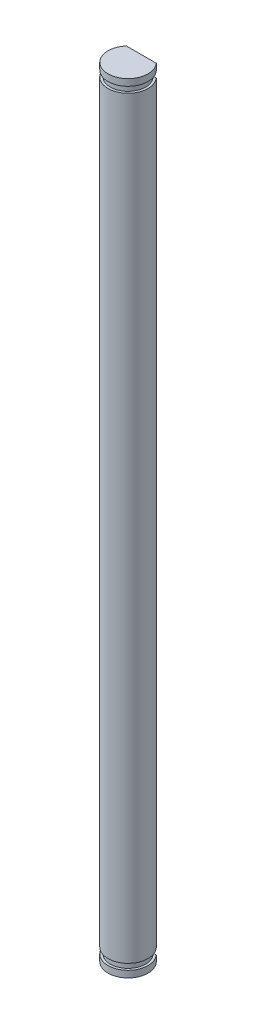
SolidWorks part; units mm, degrees
ref_plane "Front Plane" through (0, 0, 0) normal (0, 0, 1) x (1, 0, 0)
ref_plane "Top Plane" through (0, 0, 0) normal (0, 1, 0) x (1, 0, 0)
ref_plane "Right Plane" through (0, 0, 0) normal (1, 0, 0) x (0, 0, -1)
sketch "Sketch1" plane through (0, 0, 0) normal (0, 1, 0) x (1, 0, 0)
  line L0 (-2.2361, 2) -> (2.2361, 2)
  arc A0 (2.2361, 2) -> (-2.2361, 2) centre (0, 0) cw
  dimension "D1" = 3
  dimension "D2" = 2
extrude "Boss-Extrude1" add sketch "Sketch1" along normal mid plane 116.84
sketch "Sketch2" plane through (0, 0, 0) normal (0, 0, 1) x (1, 0, 0)
  line L8 (3, 56.52) -> (3, -56.52) construction
  line L9 (2.65, 57.42) -> (3, 57.42)
  line L10 (2.65, 57.42) -> (2.65, 56.52)
  line L11 (2.65, 56.52) -> (3, 56.52)
  line L12 (3, 57.42) -> (3, 56.52)
  line L13 (2.65, -56.52) -> (3, -56.52)
  line L14 (2.65, -56.52) -> (2.65, -57.42)
  line L15 (2.65, -57.42) -> (3, -57.42)
  line L16 (3, -56.52) -> (3, -57.42)
  line L17 (3, 58.42) -> (-3, 58.42) construction
  line L18 (0, 48.0561) -> (0, -49951.9439) construction
  point P8 (3, 0)
  dimension "D1" = 0.9
  dimension "D2" = 0.35
  dimension "D3" = 3
  dimension "D4" = 1
revolve "Cut-Revolve1" cut sketch "Sketch2" angle 360 about L18
